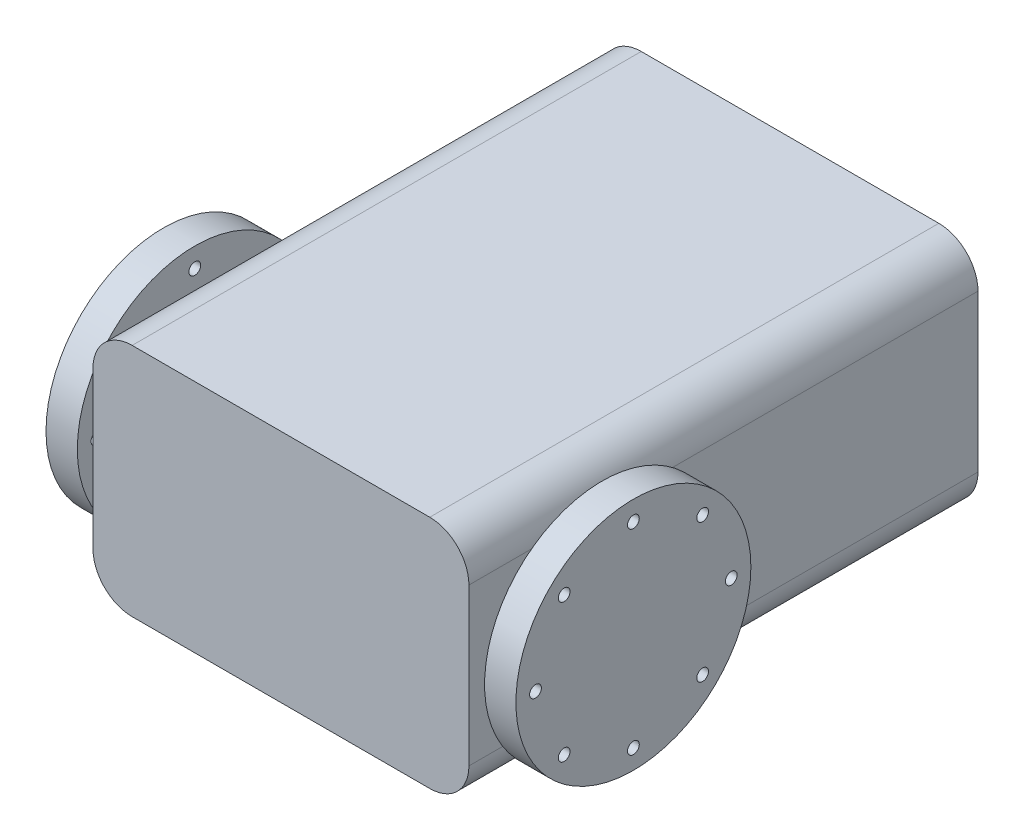
SolidWorks part; units mm, degrees
ref_plane "Front Plane" through (0, 0, 0) normal (0, 0, 1) x (1, 0, 0)
ref_plane "Top Plane" through (0, 0, 0) normal (0, 1, 0) x (1, 0, 0)
ref_plane "Right Plane" through (0, 0, 0) normal (1, 0, 0) x (0, 0, -1)
sketch "Sketch1" plane through (0, 0, 0) normal (0, 0, 1) x (1, 0, 0)
  line L1 (-19, -15) -> (19, -15)
  line L2 (-24, -10) -> (-24, 10)
  line L3 (-19, 15) -> (19, 15)
  line L4 (24, -10) -> (24, 10)
  line L5 (-24, -15) -> (24, 15) construction
  line L6 (-24, 15) -> (24, -15) construction
  arc A0 (19, 15) -> (24, 10) centre (19, 10) cw
  arc A1 (19, -15) -> (24, -10) centre (19, -10) ccw
  arc A2 (-19, -15) -> (-24, -10) centre (-19, -10) cw
  arc A3 (-19, 15) -> (-24, 10) centre (-19, 10) ccw
  point P0 (0, 0)
  dimension "D3" = 5
  dimension "D1" = 48
  dimension "D2" = 30
extrude "Boss-Extrude1" add sketch "Sketch1" along normal mid plane 65
sketch "Sketch2" plane through (24, 0, 0) normal (1, 0, 0) x (0, 0, -1)
  line L0 (-32.5, 0) -> (-17.5, 0) construction
  line L1 (-32.5, -10) -> (-32.5, 10) construction
  circle A0 centre (-17.5, 0) radius 15
  dimension "D2" = 30
  dimension "D1" = 15
extrude "Boss-Extrude2" add sketch "Sketch2" along normal blind 4 from offset 2 separate body
sketch "Sketch3" plane through (26, 0, 0) normal (-1, 0, 0) x (0, 0, 1)
  circle A0 centre (17.5, 0) radius 7.5
  dimension "D1" = 15
extrude "Boss-Extrude3" add sketch "Sketch3" along normal up to surface (50 mm away)
mirror "Mirror3" about plane through (0, 0, 0) normal (1, 0, 0) of "Boss-Extrude3"
sketch "Sketch4" plane through (-26, 0, 0) normal (-1, 0, 0) x (0, 0, 1)
  circle A0 centre (17.5, 0) radius 15
  dimension "D1" = 30
extrude "Boss-Extrude4" add sketch "Sketch4" along normal blind 4
sketch "Sketch5" plane through (30, 0, 0) normal (1, 0, 0) x (0, 0, -1)
  circle A0 centre (-17.5, 0) radius 12.5
  circle A1 centre (-17.5, 12.5) radius 0.75
  circle A2 centre (-8.6612, 8.8388) radius 0.75
  circle A3 centre (-17.5, 0) radius 12.5
  circle A4 centre (-5, 0) radius 0.75
  circle A5 centre (-17.5, 0) radius 12.5
  circle A6 centre (-8.6612, -8.8388) radius 0.75
  circle A7 centre (-17.5, 0) radius 12.5
  circle A8 centre (-17.5, -12.5) radius 0.75
  circle A9 centre (-17.5, 0) radius 12.5
  circle A10 centre (-26.3388, -8.8388) radius 0.75
  circle A11 centre (-17.5, 0) radius 12.5
  circle A12 centre (-30, 0) radius 0.75
  circle A13 centre (-17.5, 0) radius 12.5
  circle A14 centre (-26.3388, 8.8388) radius 0.75
  circle A15 centre (-17.5, 0) radius 12.5
  point P36 (-17.5, 0)
  dimension "D1" = 25
  dimension "D2" = 1.5
  dimension "D3" = 8
extrude "Cut-Extrude1" cut sketch "Sketch5" against normal up to surface (4 mm away) contours A14 | A12 | A1 | A2 | A4 | A6 | A8 | A10 up to face at (26, 0, 10)
sketch "Sketch6" plane through (-30, 0, 0) normal (-1, 0, 0) x (0, 0, 1)
  circle A2 centre (17.5, 12.5) radius 0.75
  circle A3 centre (17.5, 0) radius 12.5
  circle A4 centre (17.5, 0) radius 12.5
  circle A5 centre (26.3388, 8.8388) radius 0.75
  circle A6 centre (17.5, 0) radius 12.5
  circle A7 centre (30, 0) radius 0.75
  circle A8 centre (17.5, 0) radius 12.5
  circle A9 centre (26.3388, -8.8388) radius 0.75
  circle A10 centre (17.5, 0) radius 12.5
  circle A11 centre (17.5, -12.5) radius 0.75
  circle A12 centre (17.5, 0) radius 12.5
  circle A13 centre (8.6612, -8.8388) radius 0.75
  circle A14 centre (17.5, 0) radius 12.5
  circle A15 centre (5, 0) radius 0.75
  circle A16 centre (17.5, 0) radius 12.5
  circle A17 centre (8.6612, 8.8388) radius 0.75
  circle A18 centre (17.5, 0) radius 12.5
  point P38 (17.5, 0)
  dimension "D2" = 1.5
  dimension "D1" = 2.5
  dimension "D3" = 8
extrude "Cut-Extrude2" cut sketch "Sketch6" against normal blind 4 contours A17 | A2 | A5 | A7 | A9 | A11 | A13 | A15
